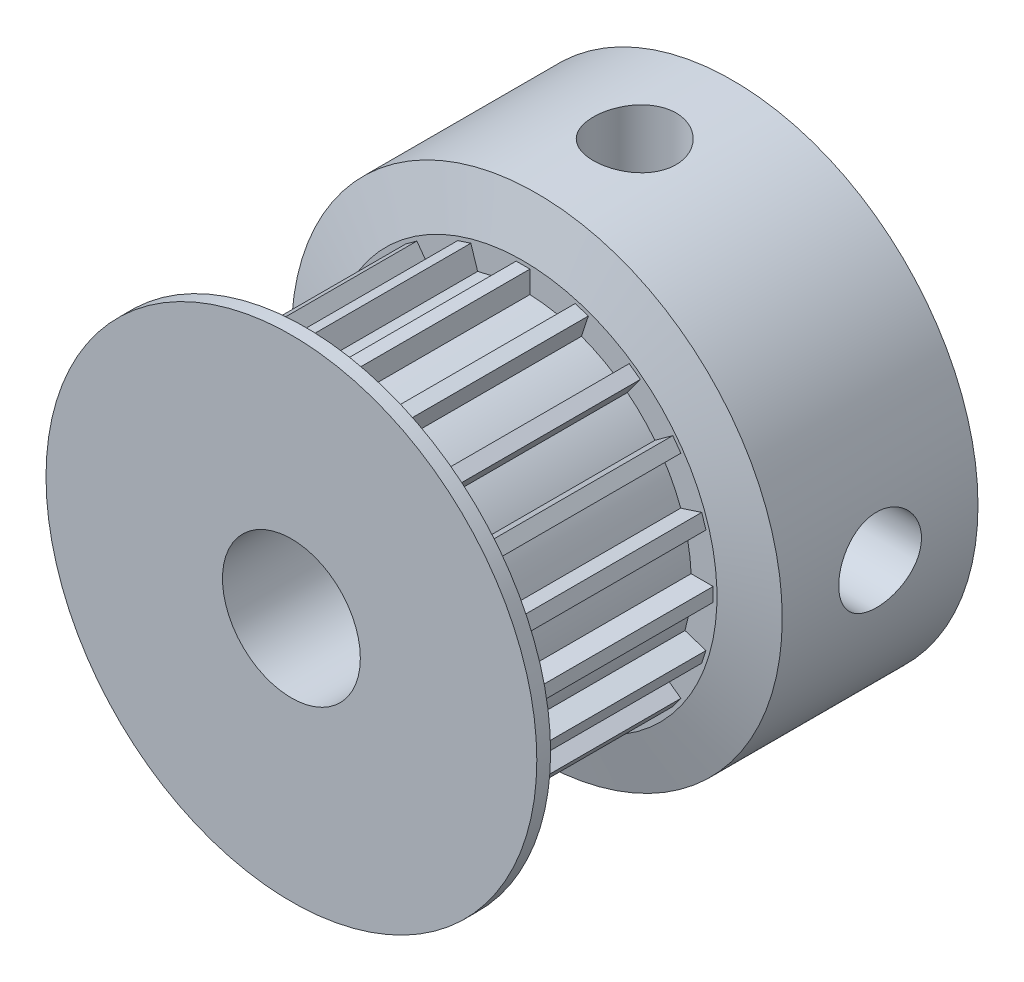
SolidWorks part; units mm, degrees
ref_plane "Front Plane" through (0, 0, 0) normal (0, 0, 1) x (1, 0, 0)
ref_plane "Top Plane" through (0, 0, 0) normal (0, 1, 0) x (1, 0, 0)
ref_plane "Right Plane" through (0, 0, 0) normal (1, 0, 0) x (0, 0, -1)
sketch "Sketch2" plane through (0, 0, 0) normal (1, 0, 0) x (0, 0, -1)
  line L0 (-16, 2.5) -> (0, 2.5)
  line L1 (0, 2.5) -> (0, 8.9)
  line L2 (0, 8.9) -> (-7.6, 8.9)
  line L3 (-7.6, 8.9) -> (-7.6, 6.1)
  line L4 (-7.6, 6.1) -> (-15, 6.1)
  line L5 (-15, 6.1) -> (-15, 8.9)
  line L6 (-15, 8.9) -> (-16, 8.9)
  line L7 (-16, 8.9) -> (-16, 2.5)
  line L8 (-79.6095, 0) -> (75.5553, 0) construction
  dimension "D1" = 16
  dimension "D2" = 8.9
  dimension "D3" = 1
  dimension "D4" = 7.4
  dimension "D5" = 2.5
  dimension "D6" = 6.1
revolve "Revolve1" add sketch "Sketch2" angle 360 about L8
chamfer "Chamfer1" distance 0.5 angle 75 1 edges at (8.9, 0, 15)
chamfer "Chamfer2" distance 0.5 angle 75 1 edges at (8.9, 0, 7.6)
sketch "Sketch4" plane through (0, 0, 7.6) normal (0, 0, 1) x (1, 0, 0)
  line L0 (1.6457, 5.8738) -> (1.8929, 6.6347)
  line L1 (1.8929, 6.6347) -> (2.3684, 6.4802)
  line L2 (-0.25, 6.0949) -> (-0.25, 6.8949)
  line L3 (-0.25, 6.8949) -> (0.25, 6.8949)
  line L4 (0.25, 6.0949) -> (0.25, 6.8949)
  line L5 (2.1212, 5.7193) -> (2.3684, 6.4802)
  line L6 (3.3802, 5.0778) -> (3.8505, 5.725)
  line L7 (3.8505, 5.725) -> (4.255, 5.4311)
  line L8 (3.7847, 4.7839) -> (4.255, 5.4311)
  line L9 (4.7839, 3.7847) -> (5.4311, 4.255)
  line L10 (5.4311, 4.255) -> (5.725, 3.8505)
  line L11 (5.0778, 3.3802) -> (5.725, 3.8505)
  line L12 (5.7193, 2.1212) -> (6.4802, 2.3684)
  line L13 (6.4802, 2.3684) -> (6.6347, 1.8929)
  line L14 (5.8738, 1.6457) -> (6.6347, 1.8929)
  line L15 (6.0949, 0.25) -> (6.8949, 0.25)
  line L16 (6.8949, 0.25) -> (6.8949, -0.25)
  line L17 (6.0949, -0.25) -> (6.8949, -0.25)
  line L18 (5.8738, -1.6457) -> (6.6347, -1.8929)
  line L19 (6.6347, -1.8929) -> (6.4802, -2.3684)
  line L20 (5.7193, -2.1212) -> (6.4802, -2.3684)
  line L21 (5.0778, -3.3802) -> (5.725, -3.8505)
  line L22 (5.725, -3.8505) -> (5.4311, -4.255)
  line L23 (4.7839, -3.7847) -> (5.4311, -4.255)
  line L24 (3.7847, -4.7839) -> (4.255, -5.4311)
  line L25 (4.255, -5.4311) -> (3.8505, -5.725)
  line L26 (3.3802, -5.0778) -> (3.8505, -5.725)
  line L27 (2.1212, -5.7193) -> (2.3684, -6.4802)
  line L28 (2.3684, -6.4802) -> (1.8929, -6.6347)
  line L29 (1.6457, -5.8738) -> (1.8929, -6.6347)
  line L30 (0.25, -6.0949) -> (0.25, -6.8949)
  line L31 (0.25, -6.8949) -> (-0.25, -6.8949)
  line L32 (-0.25, -6.0949) -> (-0.25, -6.8949)
  line L33 (-1.6457, -5.8738) -> (-1.8929, -6.6347)
  line L34 (-1.8929, -6.6347) -> (-2.3684, -6.4802)
  line L35 (-2.1212, -5.7193) -> (-2.3684, -6.4802)
  line L36 (-3.3802, -5.0778) -> (-3.8505, -5.725)
  line L37 (-3.8505, -5.725) -> (-4.255, -5.4311)
  line L38 (-3.7847, -4.7839) -> (-4.255, -5.4311)
  line L39 (-4.7839, -3.7847) -> (-5.4311, -4.255)
  line L40 (-5.4311, -4.255) -> (-5.725, -3.8505)
  line L41 (-5.0778, -3.3802) -> (-5.725, -3.8505)
  line L42 (-5.7193, -2.1212) -> (-6.4802, -2.3684)
  line L43 (-6.4802, -2.3684) -> (-6.6347, -1.8929)
  line L44 (-5.8738, -1.6457) -> (-6.6347, -1.8929)
  line L45 (-6.0949, -0.25) -> (-6.8949, -0.25)
  line L46 (-6.8949, -0.25) -> (-6.8949, 0.25)
  line L47 (-6.0949, 0.25) -> (-6.8949, 0.25)
  line L48 (-5.8738, 1.6457) -> (-6.6347, 1.8929)
  line L49 (-6.6347, 1.8929) -> (-6.4802, 2.3684)
  line L50 (-5.7193, 2.1212) -> (-6.4802, 2.3684)
  line L51 (-5.0778, 3.3802) -> (-5.725, 3.8505)
  line L52 (-5.725, 3.8505) -> (-5.4311, 4.255)
  line L53 (-4.7839, 3.7847) -> (-5.4311, 4.255)
  line L54 (-3.7847, 4.7839) -> (-4.255, 5.4311)
  line L55 (-4.255, 5.4311) -> (-3.8505, 5.725)
  line L56 (-3.3802, 5.0778) -> (-3.8505, 5.725)
  line L57 (-2.1212, 5.7193) -> (-2.3684, 6.4802)
  line L58 (-2.3684, 6.4802) -> (-1.8929, 6.6347)
  line L59 (-1.6457, 5.8738) -> (-1.8929, 6.6347)
  arc A0 (-3.3802, 5.0778) -> (-3.7847, 4.7839) centre (0, 0) ccw
  arc A1 (-1.6457, 5.8738) -> (-2.1212, 5.7193) centre (0, 0) ccw
  arc A2 (0.25, 6.0949) -> (-0.25, 6.0949) centre (0, 0) ccw
  arc A3 (2.1212, 5.7193) -> (1.6457, 5.8738) centre (0, 0) ccw
  arc A4 (3.7847, 4.7839) -> (3.3802, 5.0778) centre (0, 0) ccw
  arc A5 (5.0778, 3.3802) -> (4.7839, 3.7847) centre (0, 0) ccw
  arc A6 (5.8738, 1.6457) -> (5.7193, 2.1212) centre (0, 0) ccw
  arc A7 (6.0949, -0.25) -> (6.0949, 0.25) centre (0, 0) ccw
  arc A8 (5.7193, -2.1212) -> (5.8738, -1.6457) centre (0, 0) ccw
  arc A9 (4.7839, -3.7847) -> (5.0778, -3.3802) centre (0, 0) ccw
  arc A10 (3.3802, -5.0778) -> (3.7847, -4.7839) centre (0, 0) ccw
  arc A11 (1.6457, -5.8738) -> (2.1212, -5.7193) centre (0, 0) ccw
  arc A12 (-0.25, -6.0949) -> (0.25, -6.0949) centre (0, 0) ccw
  arc A13 (-2.1212, -5.7193) -> (-1.6457, -5.8738) centre (0, 0) ccw
  arc A14 (-3.7847, -4.7839) -> (-3.3802, -5.0778) centre (0, 0) ccw
  arc A15 (-5.0778, -3.3802) -> (-4.7839, -3.7847) centre (0, 0) ccw
  arc A16 (-5.8738, -1.6457) -> (-5.7193, -2.1212) centre (0, 0) ccw
  arc A17 (-6.0949, 0.25) -> (-6.0949, -0.25) centre (0, 0) ccw
  arc A18 (-5.7193, 2.1212) -> (-5.8738, 1.6457) centre (0, 0) ccw
  arc A19 (-4.7839, 3.7847) -> (-5.0778, 3.3802) centre (0, 0) ccw
  dimension "D1" = 12.2
  dimension "D2" = 0.5
  dimension "D3" = 0.25
  dimension "D4" = 0.8
  dimension "D5" = 20
extrude "Boss-Extrude1" add sketch "Sketch4" along normal up to surface (7.4 mm away) up to face at (7.034, 0, 15)
ref_plane "Plane1" through (0, 8.9, 0) normal (0, 1, 0) x (-1, 0, 0)
sketch "Sketch6" plane through (0, 8.9, 0) normal (0, 1, 0) x (-1, 0, 0)
  line L2 (0, 3.55) -> (4.2063, 3.55) construction
  circle A0 centre (0, 3.55) radius 1.5
  dimension "D1" = 3
  dimension "D2" = 3.55
extrude "Cut-Extrude1" cut sketch "Sketch6" against normal blind 10
pattern_circular "CirPattern1" count 2 every 270 about axis through (0, 0, 0) along (0, 0, 1) of "Cut-Extrude1"
